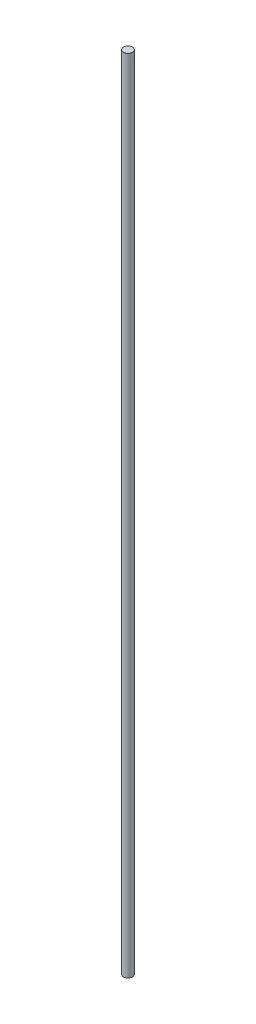
SolidWorks part; units mm, degrees
ref_plane "Front Plane" through (0, 0, 0) normal (0, 0, 1) x (1, 0, 0)
ref_plane "Top Plane" through (0, 0, 0) normal (0, 1, 0) x (1, 0, 0)
ref_plane "Right Plane" through (0, 0, 0) normal (1, 0, 0) x (0, 0, -1)
sketch "Sketch1" plane through (0, 0, 0) normal (0, 1, 0) x (1, 0, 0)
  circle A0 centre (0, 0) radius 3.175
  dimension "D1" = 6.35
extrude "Boss-Extrude1" add sketch "Sketch1" along normal blind 558.8
